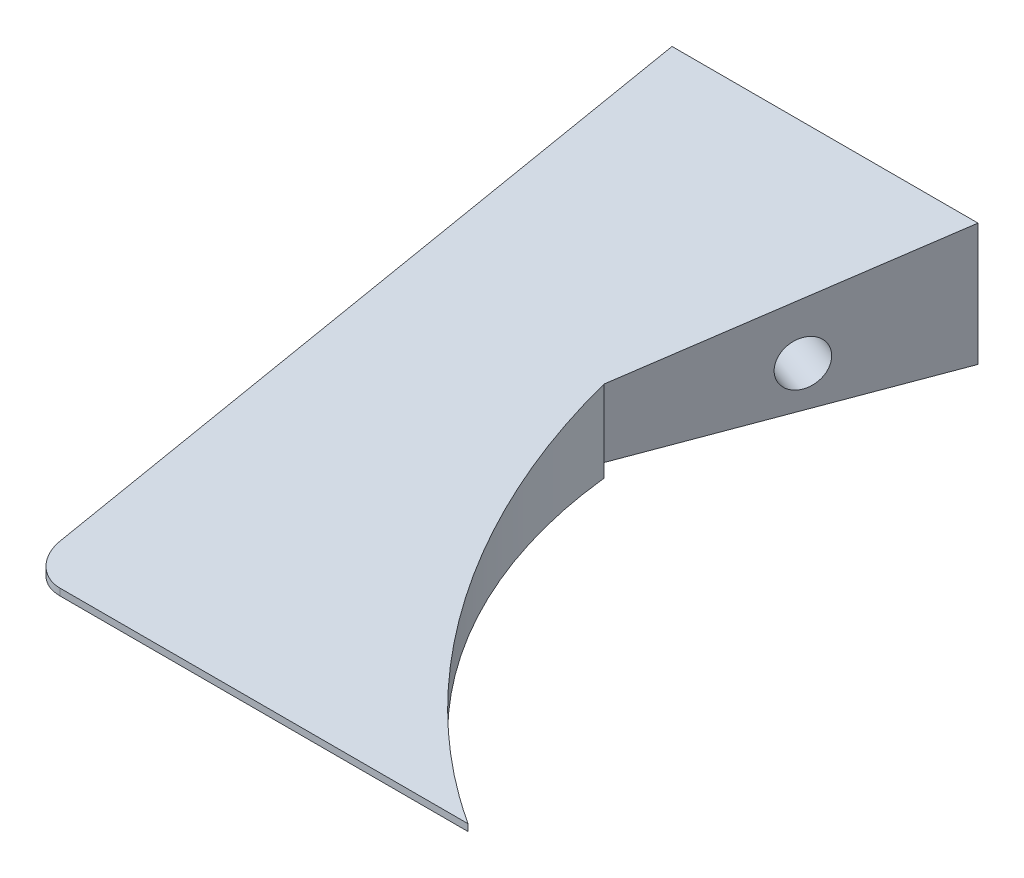
SolidWorks part; units mm, degrees
material "AISI 1020"
ref_plane "Plano frontal" through (0, 0, 0) normal (0, 0, 1) x (1, 0, 0)
ref_plane "Plano superior" through (0, 0, 0) normal (0, 1, 0) x (1, 0, 0)
ref_plane "Plano direito" through (0, 0, 0) normal (1, 0, 0) x (0, 0, -1)
sketch "Esboço1" plane through (0, 0, 0) normal (0, 0, 1) x (1, 0, 0)
  line L1 (-65, 10) -> (65, 10)
  line L2 (-65, 10) -> (-65, -10)
  line L3 (-65, -10) -> (65, -10)
  line L4 (65, 10) -> (65, -10)
  line L5 (-65, 10) -> (65, -10) construction
  line L6 (-65, -10) -> (65, 10) construction
  point P0 (0, 0)
  dimension "D1" = 130
  dimension "D2" = 20
extrude "Ressalto-extrusão1" add sketch "Esboço1" along normal blind 95
sketch "Esboço2" plane through (0, 10, 0) normal (0, 1, 0) x (1, 0, 0)
  line L0 (65, 0) -> (-20, 0)
  line L2 (-65, -95) -> (-65, 0) construction
  line L3 (-35, -40) -> (-20, 0)
  line L4 (65, 0) -> (-65, 0) construction
  line L10 (65, -95) -> (-65, -95) construction
  line L11 (0, -95) -> (65, -95)
  line L12 (65, -95) -> (65, 0)
  arc A1 (0, -95) -> (-35, -40) centre (38.051, -32.1494) cw
  dimension "D4" = 73.4716
  dimension "D5" = 40
  dimension "D1" = 45
  dimension "D2" = 30
  dimension "D3" = 65
extrude "Corte-extrusão2" cut sketch "Esboço2" against normal up to next contours L3 L0 L12 L11 A1
sketch "Esboço13" plane through (-65, 0, 0) normal (-1, 0, 0) x (0, 0, 1)
  line L0 (0, 10) -> (95, -9)
  line L1 (95, 10) -> (95, -10) construction
  dimension "D1" = 1
extrude "Corte-extrusão4" cut sketch "Esboço13" against normal through all and the other way through all
hole_wizard "Broca de rosquear de cano para tarraxa de 1/84" positions "Esboço14" profile "Esboço15" hole size "1/8" standard "Ansi Inch"
sketch "Esboço14" plane through (-65, 0, 0) normal (-1, 0, 0) x (0, 0, 1)
  line L0 (0, 10) -> (0, -10) construction
  line L1 (95, -10) -> (0, -10) construction
  point P0 (20, -2)
  dimension "D1" = 20
  dimension "D2" = 8
sketch "Esboço15" plane through (-65, -2, 20) normal (0, 1, 0) x (0, 0, 1)
  line L0 (0, 0) -> (0, 11.9768)
  line L1 (0, 11.9768) -> (3.29, 10)
  line L2 (3.29, 10) -> (3.29, 0)
  line L5 (3.29, 0) -> (0, 0)
  line L10 (0, 11.9768) -> (-3.29, 10) construction
  line L11 (0, -6.35) -> (0, 107.95) construction
  dimension "Hole Dia." = 6.58
  dimension "Hole Depth" = 10
  dimension "Drill Angle" = 118
hole_wizard "Broca de rosquear de cano para tarraxa de 1/85" positions "Esboço16" profile "Esboço17" hole size "1/8" standard "Ansi Inch"
sketch "Esboço16" plane through (-17.5342, 0, -6.5753) normal (0.9363, 0, 0.3511) x (0.3511, 0, -0.9363)
  line L0 (-7.0225, -10) -> (-7.0225, 10) construction
  line L1 (-7.0225, -10) -> (-49.7425, -10) construction
  point P0 (-27.0225, -2)
  dimension "D1" = 20
  dimension "D2" = 8
sketch "Esboço17" plane through (-27.0225, -2, 18.7266) normal (0, 1, 0) x (0.3511, 0, -0.9363)
  line L0 (0, 0) -> (0, 11.9768)
  line L1 (0, 11.9768) -> (3.29, 10)
  line L2 (3.29, 10) -> (3.29, 0)
  line L5 (3.29, 0) -> (0, 0)
  line L10 (0, 11.9768) -> (-3.29, 10) construction
  line L11 (0, -6.35) -> (0, 107.95) construction
  dimension "Hole Dia." = 6.58
  dimension "Hole Depth" = 10
  dimension "Drill Angle" = 118
fillet "Filete2" radius 5 1 edges at (-65, -9.5, 95)
sketch "Esboço38" plane through (0, 0, 0) normal (0, 0, -1) x (-1, 0, 0)
  line L0 (20, -8) -> (65, -8)
  line L1 (20, -10) -> (20, 10) construction
  line L2 (65, 10) -> (65, -10) construction
  line L3 (65, -8) -> (65, -10)
  line L4 (65, -10) -> (20, -10)
  line L5 (0, -10) -> (35, -10) construction
  line L6 (65, -10) -> (20, -10) construction
  line L7 (20, -10) -> (20, -8)
  dimension "D1" = 2
extrude "Corte-extrusão9" cut sketch "Esboço38" against normal blind 40
